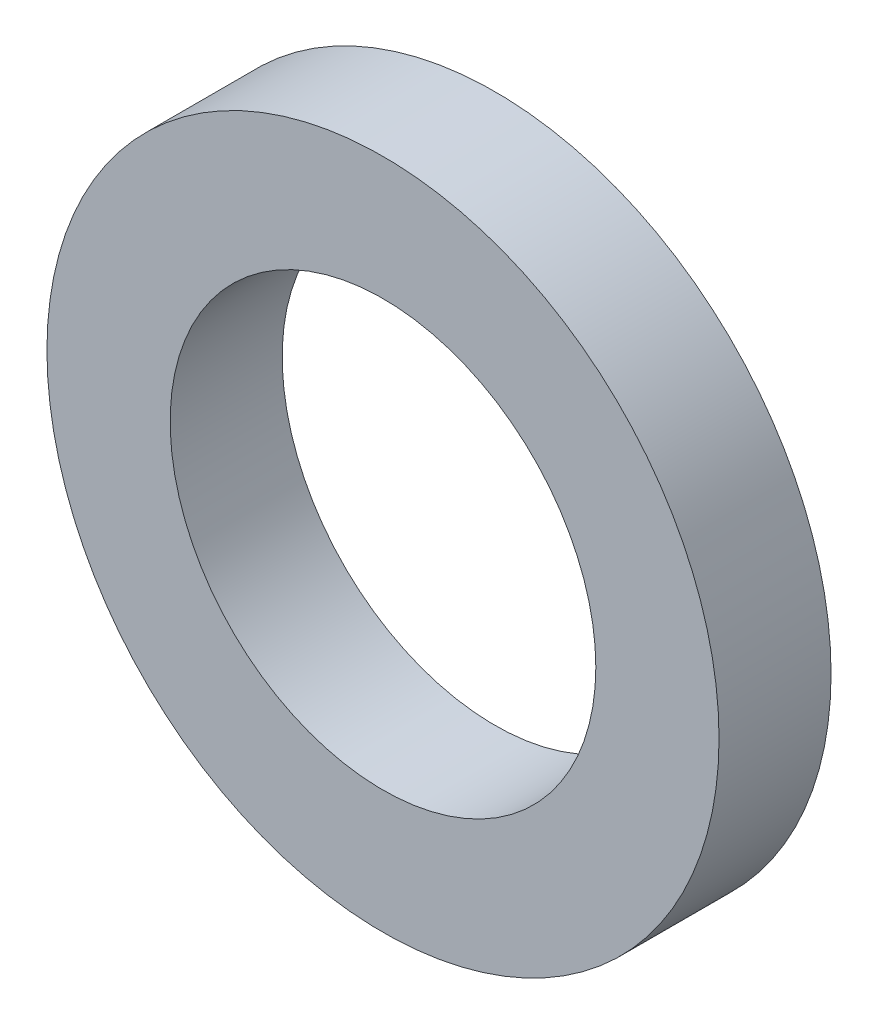
SolidWorks part; units mm, degrees
ref_plane "Front Plane" through (0, 0, 0) normal (0, 0, 1) x (1, 0, 0)
ref_plane "Top Plane" through (0, 0, 0) normal (0, 1, 0) x (1, 0, 0)
ref_plane "Right Plane" through (0, 0, 0) normal (1, 0, 0) x (0, 0, -1)
sketch "Эскиз1" plane through (0, 0, 0) normal (0, 0, 1) x (1, 0, 0)
  circle A0 centre (0, 0) radius 1.9
  circle A1 centre (0, 0) radius 3
  dimension "D1" = 3.8
  dimension "D2" = 6
extrude "Бобышка-Вытянуть1" add sketch "Эскиз1" along normal blind 1
